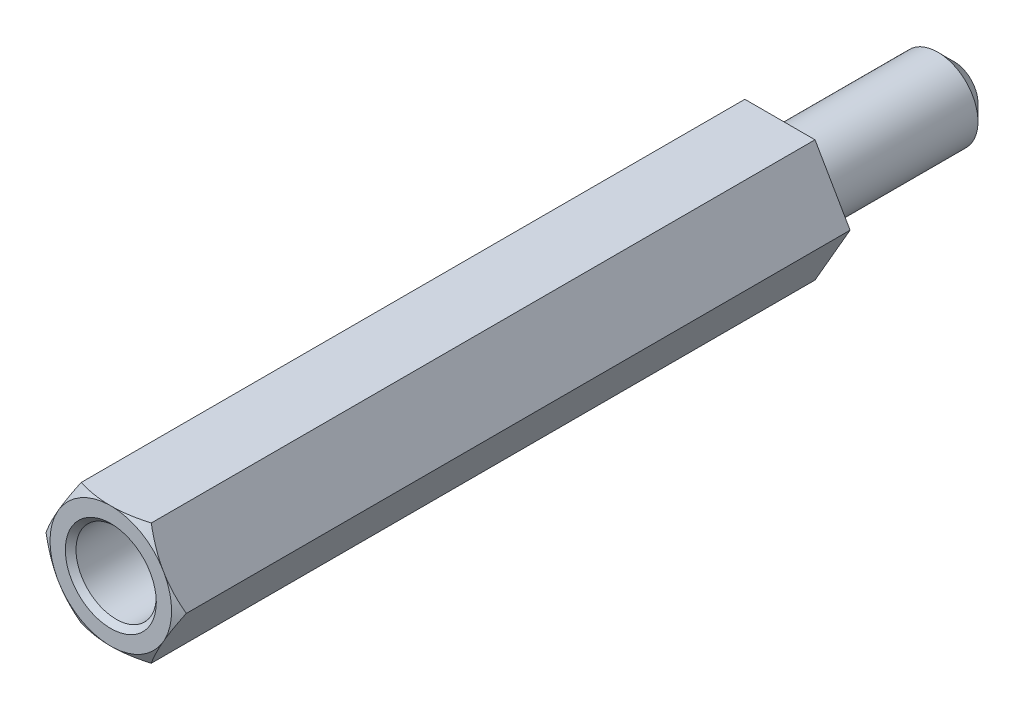
SolidWorks part; units mm, degrees
ref_plane "Front Plane" through (0, 0, 0) normal (0, 0, 1) x (1, 0, 0)
ref_plane "Top Plane" through (0, 0, 0) normal (0, 1, 0) x (1, 0, 0)
ref_plane "Right Plane" through (0, 0, 0) normal (1, 0, 0) x (0, 0, -1)
sketch "Sketch1" plane through (0, 0, 0) normal (0, 0, 1) x (1, 0, 0)
  line L0 (0, 0) -> (2.6212, 0) construction
  line L1 (2.6212, 0) -> (1.3106, 2.27)
  line L2 (1.3106, 2.27) -> (-1.3106, 2.27)
  line L3 (-1.3106, 2.27) -> (-2.6212, 0)
  line L4 (-2.6212, 0) -> (-1.3106, -2.27)
  line L5 (-1.3106, -2.27) -> (1.3106, -2.27)
  line L6 (1.3106, -2.27) -> (2.6212, 0)
  circle A0 centre (0, 0) radius 2.27 construction
  dimension "D1" = 4.54
extrude "Boss-Extrude1" add sketch "Sketch1" along normal blind 25
sketch "Sketch2" plane through (0, 0, 25) normal (0, 0, 1) x (1, 0, 0)
  circle A0 centre (0, 0) radius 1.5
extrude "Cut-Extrude1" cut sketch "Sketch2" against normal blind 12 and the other way through all
sketch "Sketch3" plane through (0, 0, 0) normal (0, 1, 0) x (1, 0, 0)
  line L0 (-2.6212, -25) -> (-2.2712, -25)
  line L1 (-2.2712, -25) -> (-2.6212, -24.8)
  line L2 (-2.6212, -25) -> (-2.6212, 0) construction
  line L3 (-2.6212, -24.8) -> (-2.6212, -25)
  dimension "D1" = 0.35
  dimension "D2" = 0.2
ref_axis "Axis1" through (0, 0, 13) along (0, 0, 1)
revolve "Cut-Revolve1" cut sketch "Sketch3" angle 360 about axis through (0, 0, 13) along (0, 0, 1)
ref_plane "Plane1" through (0, 0, 12.5) normal (0, 0, 1) x (1, 0, 0)
chamfer "Chamfer1" distance 0.2 angle 45 1 edges at (1.5, 0, 25)
sketch "Sketch4" plane through (0, 0, 0) normal (0, 0, -1) x (-1, 0, 0)
  circle A0 centre (0, 0) radius 1.5
extrude "Boss-Extrude2" add sketch "Sketch4" along normal blind 6.5
chamfer "Chamfer2" distance 0.6 angle 45 1 edges at (-1.5, 0, -6.5)
